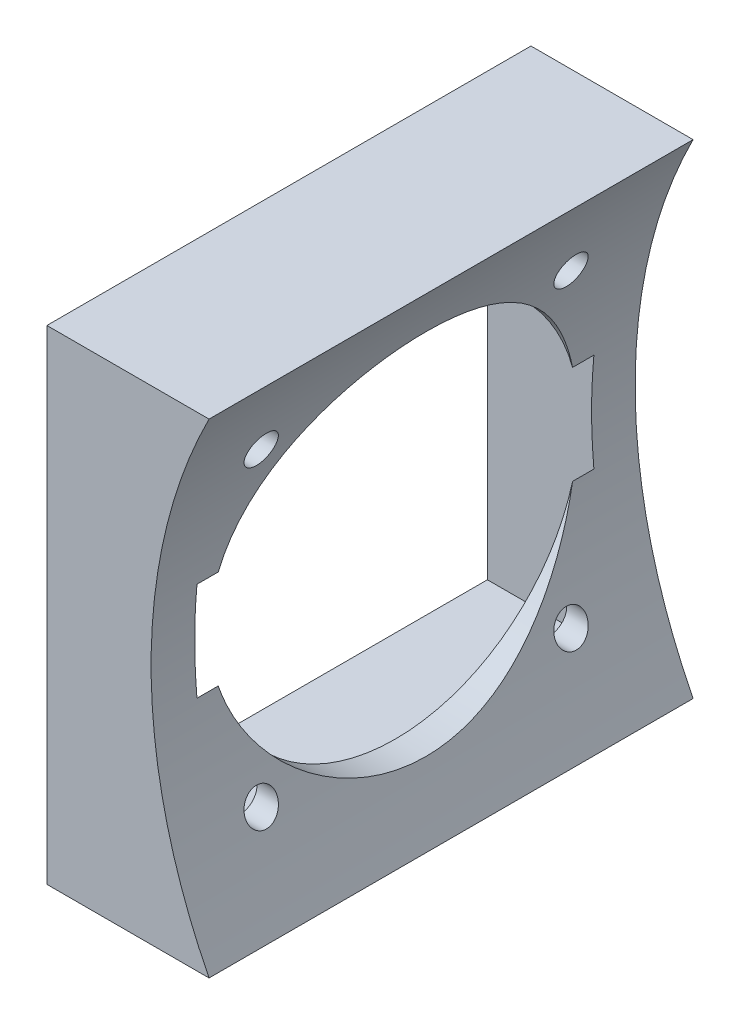
SolidWorks part; units mm, degrees
material "PLA"
ref_plane "Alzado" through (0, 0, 0) normal (0, 0, 1) x (1, 0, 0)
ref_plane "Planta" through (0, 0, 0) normal (0, 1, 0) x (1, 0, 0)
ref_plane "Vista lateral" through (0, 0, 0) normal (1, 0, 0) x (0, 0, -1)
sketch "Croquis1" plane through (0, 0, 0) normal (0, 0, 1) x (1, 0, 0)
  line L1 (8.375, -25) -> (-8.375, -25)
  line L3 (8.375, 25) -> (-8.375, 25)
  line L4 (-8.375, -25) -> (-8.375, 25)
  line L5 (8.375, -25) -> (-8.375, 25) construction
  line L6 (8.375, 25) -> (-8.375, -25) construction
  arc A0 (8.375, 25) -> (8.375, -25) centre (57.5892, 0) ccw
  point P0 (0, 0)
  dimension "D3" = 55.2
  dimension "D1" = 50
  dimension "D2" = 16.75
extrude "Saliente-Extruir1" add sketch "Croquis1" along normal blind 50
sketch "Croquis2" plane through (-8.375, 0, 0) normal (-1, 0, 0) x (0, 0, 1)
  line L0 (25, 25) -> (25, -25) construction
  line L1 (45.5, -20.5) -> (4.5, -20.5)
  line L2 (45.5, -20.5) -> (45.5, 20.5)
  line L3 (45.5, 20.5) -> (4.5, 20.5)
  line L4 (4.5, -20.5) -> (4.5, 20.5)
  line L5 (45.5, -20.5) -> (4.5, 20.5) construction
  line L6 (45.5, 20.5) -> (4.5, -20.5) construction
  line L7 (50, 25) -> (0, 25) construction
  line L8 (50, -25) -> (0, -25) construction
  line L9 (0, 0) -> (50, 0) construction
  line L10 (50, 25) -> (50, -25) construction
  point P0 (25, 0)
  dimension "D1" = 41
extrude "Cortar-Extruir1" cut sketch "Croquis2" against normal blind 11
sketch "Croquis3" plane through (2.625, 0, 0) normal (-1, 0, 0) x (0, 0, 1)
  line L0 (25, 20.5) -> (25, -20.5) construction
  line L1 (41, -16) -> (9, -16) construction
  line L2 (41, -16) -> (41, 16) construction
  line L3 (41, 16) -> (9, 16) construction
  line L4 (9, -16) -> (9, 16) construction
  line L5 (41, -16) -> (9, 16) construction
  line L6 (41, 16) -> (9, -16) construction
  line L7 (45.5, 20.5) -> (4.5, 20.5) construction
  line L8 (4.5, -20.5) -> (45.5, -20.5) construction
  line L9 (50, -25) -> (0, -25) construction
  circle A0 centre (9, 16) radius 1.7
  circle A1 centre (41, 16) radius 1.7
  circle A2 centre (41, -16) radius 1.7
  circle A3 centre (9, -16) radius 1.7
  circle A4 centre (25, 0) radius 19
  point P0 (25, 0)
  dimension "D2" = 3.4
  dimension "D3" = 38
  dimension "D1" = 32
  dimension "D4" = 9
extrude "Cortar-Extruir2" cut sketch "Croquis3" against normal blind 11
